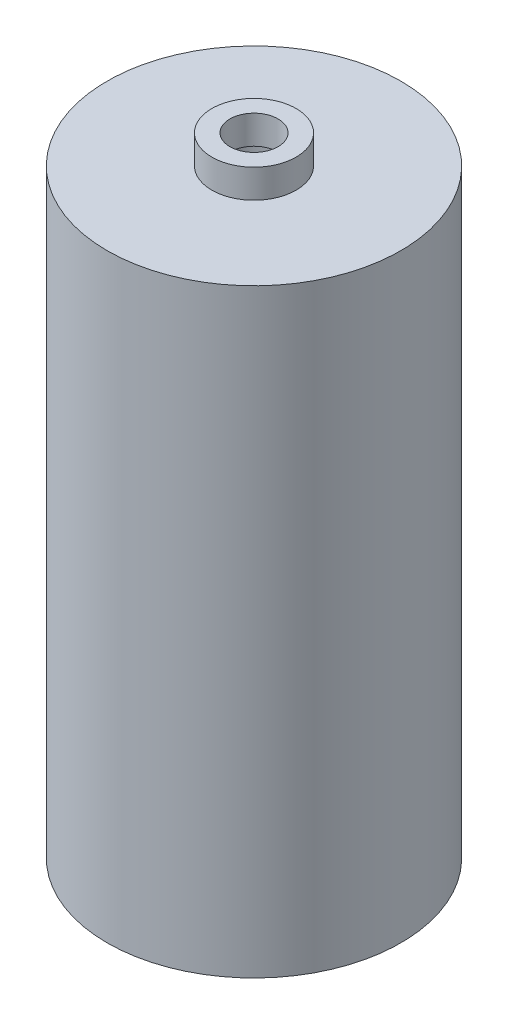
SolidWorks part; units mm, degrees
ref_plane "Front Plane" through (0, 0, 0) normal (0, 0, 1) x (1, 0, 0)
ref_plane "Top Plane" through (0, 0, 0) normal (0, 1, 0) x (1, 0, 0)
ref_plane "Right Plane" through (0, 0, 0) normal (1, 0, 0) x (0, 0, -1)
sketch "Sketch3" plane through (0, 0, 0) normal (0, 1, 0) x (1, 0, 0)
  circle A0 centre (0, 0) radius 12.2
  circle A1 centre (0, 0) radius 3.2
  dimension "D1" = 24.4
  dimension "D2" = 6.4
extrude "Boss-Extrude1" add sketch "Sketch3" along normal blind 49.8
sketch "Sketch4" plane through (0, 49.8, 0) normal (0, 1, 0) x (1, 0, 0)
  circle A0 centre (0, 0) radius 3.5
  circle A1 centre (0, 0) radius 2
  dimension "D1" = 7
  dimension "D2" = 4
extrude "Boss-Extrude2" add sketch "Sketch4" along normal blind 2.38 contours A0 | A1
